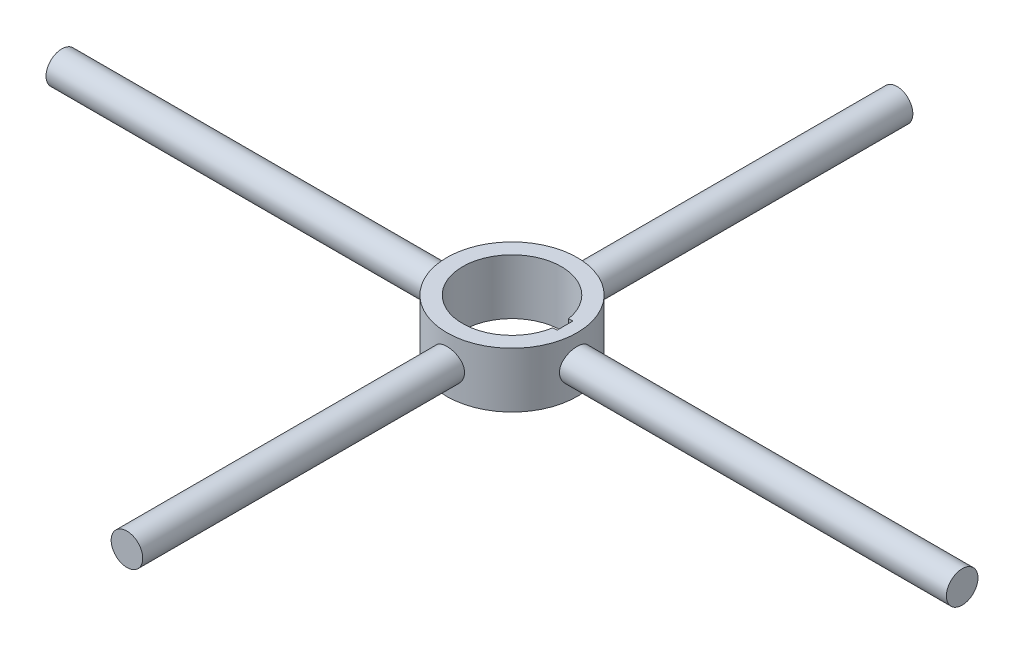
SolidWorks part; units mm, degrees
ref_plane "정면" through (0, 0, 0) normal (0, 0, 1) x (1, 0, 0)
ref_plane "평면" through (0, 0, 0) normal (0, 1, 0) x (1, 0, 0)
ref_plane "우측면" through (0, 0, 0) normal (1, 0, 0) x (0, 0, -1)
sketch "스케치1" plane through (0, 0, 0) normal (0, 1, 0) x (1, 0, 0)
  line L1 (61.6948, -10) -> (67, -10)
  line L2 (61.6948, 10) -> (67, 10)
  line L4 (67, 10) -> (67, -10)
  arc A0 (61.6948, 10) -> (61.6948, -10) centre (0, 0) ccw
  circle A1 centre (0, 0) radius 82.5
  point P1 (0, 0)
  dimension "D1" = 165
  dimension "D2" = 62.5
  dimension "D3" = 67
  dimension "D4" = 10
  dimension "D5" = 10
extrude "보스-돌출1" add sketch "스케치1" along normal blind 70
ref_plane "평면1" through (0, 0, 487.5) normal (0, 0, 1) x (1, 0, 0)
sketch "스케치2" plane through (0, 0, 487.5) normal (0, 0, 1) x (1, 0, 0)
  line L0 (0, 70) -> (0, 0) construction
  line L1 (82.5, 70) -> (-82.5, 70) construction
  line L2 (-20, 35) -> (20, 35) construction
  circle A0 centre (0, 35) radius 20
  dimension "D1" = 40
extrude "보스-돌출2" add sketch "스케치2" against normal up to next
ref_plane "평면2" through (570, 0, 0) normal (1, 0, 0) x (0, 0, -1)
sketch "스케치4" plane through (570, 0, 0) normal (1, 0, 0) x (0, 0, -1)
  line L0 (0, 0) -> (0, 70) construction
  line L1 (82.5, 70) -> (-82.5, 70) construction
  line L2 (20, 35) -> (-20, 35) construction
  circle A0 centre (0, 35) radius 20
  dimension "D1" = 40
extrude "보스-돌출3" add sketch "스케치4" against normal up to next
pattern_circular "원형 패턴2" count 2 over 360 about axis through (0, 0, 0) along (0, 1, 0) of "보스-돌출3", "보스-돌출2"
